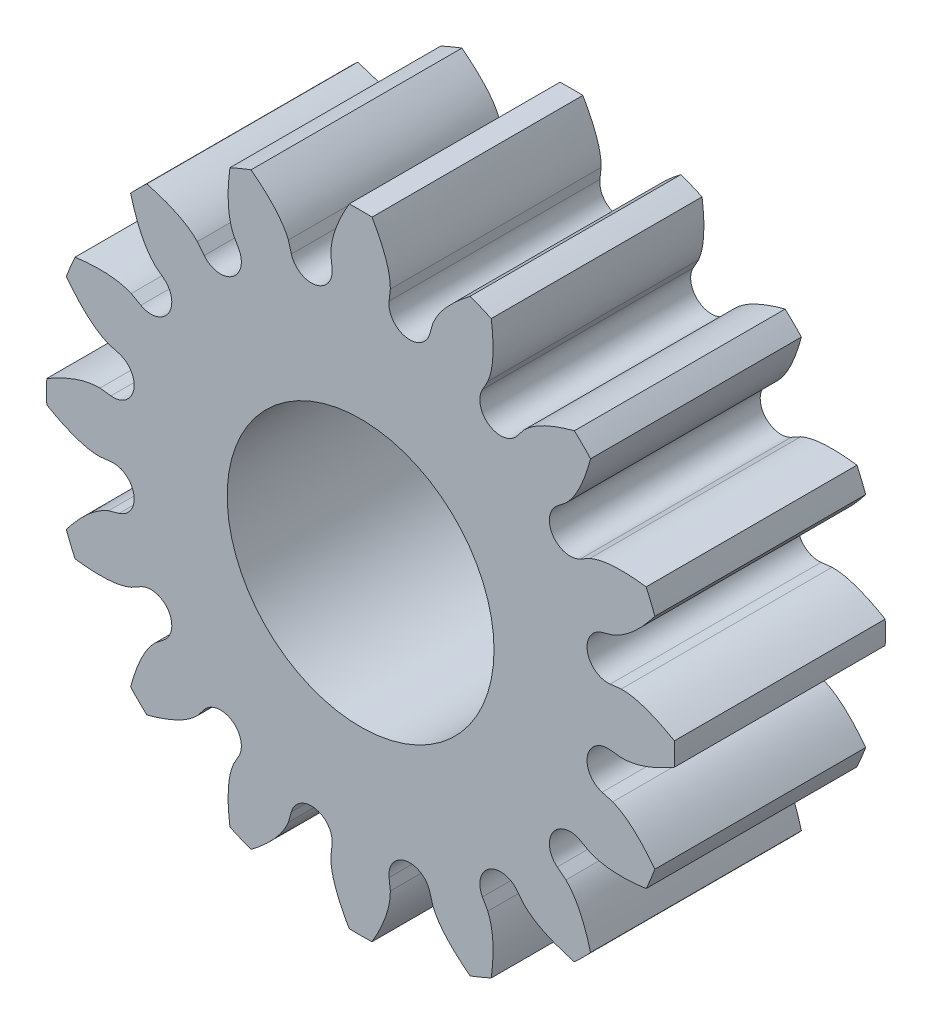
SolidWorks part; units mm, degrees
material "PE Low/Medium Density"
ref_plane "Front Plane" through (0, 0, 0) normal (0, 0, 1) x (1, 0, 0)
ref_plane "Top Plane" through (0, 0, 0) normal (0, 1, 0) x (1, 0, 0)
ref_plane "Right Plane" through (0, 0, 0) normal (1, 0, 0) x (0, 0, -1)
sketch "Involute construction sketch" plane through (0, 0, 0) normal (0, 0, 1) x (1, 0, 0)
  line L0 (0, 0) -> (-1.7884, 3.29) construction
  line L1 (0, 0) -> (-1.0853, 3.5839) construction
  line L2 (0, 0) -> (-0.3374, 3.7294) construction
  line L3 (0, 0) -> (0.4246, 3.7205) construction
  line L4 (-2.9462, 2.3113) -> (-2.4174, 2.8599) construction
  line L5 (-2.4174, 2.8599) -> (-1.7884, 3.29) construction
  line L6 (-1.7884, 3.29) -> (-1.0853, 3.5839) construction
  line L7 (0, 0) -> (-2.4174, 2.8599) construction
  line L8 (0, 0) -> (-2.9462, 2.3113) construction
  line L9 (-1.0853, 3.5839) -> (-0.3374, 3.7294) construction
  line L10 (-0.3374, 3.7294) -> (0.4246, 3.7205) construction
  line L11 (-2.9462, 2.3113) -> (-0.5946, 5.309) construction
  line L12 (-2.4174, 2.8599) -> (-0.0895, 4.8275) construction
  line L13 (-1.7884, 3.29) -> (0.2201, 4.3818) construction
  line L14 (-1.0853, 3.5839) -> (0.3732, 4.0256) construction
  line L15 (-0.3374, 3.7294) -> (0.4215, 3.7981) construction
  line L17 (0, 0) -> (0, 5.7859) construction
  line L18 (0, 0) -> (0.3906, 3.9658) construction
  line L19 (0, 0) -> (0.6442, 3.2386) construction
  circle A0 centre (0, 0) radius 3.302 construction
  circle A1 centre (0, 0) radius 3.7447 construction
  circle A2 centre (0, 0) radius 3.985 construction
  circle A3 centre (0, 0) radius 4.4831 construction
  spline S0 degree 3 poles (0.4246, 3.7205) (0.4261, 3.8242) (0.3767, 4.0544) (0.1137, 4.6484) (-0.2724, 5.0543) (-0.5946, 5.309) knots 0 0 0 0 0.160054 0.360046 1 1 1 1 construction
  point P17 (0.1633, 4.4801)
  dimension "D1" = 6.604
  dimension "D2" = 7.4893
  dimension "D3" = 7.97
  dimension "D4" = 8.9662
  dimension "D5" = 0.762
  dimension "D6" = 1.524
  dimension "D7" = 2.286
  dimension "D8" = 3.048
  dimension "D9" = 3.81
  dimension "D10" = 5.625
  dimension "D11" = 11.25
sketch "Sketch2" plane through (0, 0, 0) normal (0, 0, 1) x (1, 0, 0)
  line L0 (0, 4.4831) -> (0, 3.302)
  line L1 (0, 0) -> (0, 5.7859) construction
  line L2 (0.4246, 3.7205) -> (0.4067, 3.564)
  line L3 (0, 0) -> (0.4246, 3.7205) construction
  circle A0 centre (0, 0) radius 4.4831 construction
  circle A1 centre (0, 0) radius 3.302 construction
  arc A2 (0, 4.4831) -> (0.1633, 4.4801) centre (0, 0) cw
  arc A3 (0, 3.302) -> (0.6442, 3.2386) centre (0, 0) cw
  arc A4 (0.4067, 3.564) -> (0.6442, 3.2386) centre (0.7022, 3.5302) ccw
  spline S0 degree 3 poles (0.4246, 3.7205) (0.4258, 3.8034) (0.3801, 4.0726) (0.2566, 4.3168) (0.1633, 4.4801) knots 0 0 0 0 0.305961 1 1 1 1
sketch "Sketch3" plane through (0, 0, 0) normal (0, 0, 1) x (1, 0, 0)
  circle A0 centre (0, 0) radius 3.302
  circle A1 centre (0, 0) radius 1.905
  dimension "D1" = 6.604
  dimension "D2" = 3.81
extrude "Base" add sketch "Sketch3" along normal blind 3.0099
extrude "Half tooth" add sketch "Sketch2" along normal up to surface (3.0099 mm away) up to face at (3.302, 0, 3.0099)
ref_plane "Midplane of half tooth" through (0, 0, 0) normal (-1, 0, 0) x (0, 0, 1)
mirror "Mirror of half tooth" about plane through (0, 0, 0) normal (-1, 0, 0) of "Half tooth"
pattern_circular "Pattern of tooth" count 16 over 360 about axis through (0, 0, 3.0099) along (0, 0, 1) of "Half tooth", "Mirror of half tooth"
equation "\"radtodeg\"= 180 / PI'radian to degree conversion [ ]"
equation "\"phi\"= 20'pressure angle [deg]"
equation "\"N\"= 16'number of teeth [teeth]"
equation "\"A\"= 0.353in'diameter of addendum circle [inch]"
equation "\"B\"= 0.260in'diameter of dedendum circle [inch]"
equation "\"P\"= ( \"N\" + 2 ) / \"A\"'diametral pitch [teeth/inch]"
equation "\"d\"= \"N\" / \"P\"'diameter of pitch circle [inch]"
equation "\"cp\"= PI / \"P\"'circular pitch [inch/teeth]"
equation "\"add\"= 1 / \"P\"'addendum [inch]"
equation "\"ded\"= - ( \"B\" - \"d\" ) / 2'dedendum [inch]"
equation "\"clear\"= \"ded\" - \"add\"'clearance [inch]"
equation "\"C\"= \"B\" + 2 * \"clear\"'diameter of clearance circle [inch]"
equation "\"h\"= \"add\" + \"ded\"'tooth height / whole depth [inch]"
equation "\"s\"= \"d\" * cos ( \"phi\" * 1 / \"radtodeg\" )'diameter of base circle [inch]"
equation "\"t\"= ( PI / 2 ) / \"P\"'tooth width at diameter of pitch circle diameter [inch]"
equation "\"alpha\"= ( \"t\" / ( \"d\" / 2 ) * \"radtodeg\" ) / 2'arc angle for half of tooth width at pitch circle diameter [inch]"
equation "\"bore\"= 0.15'bore of hub [inch]"
equation "\"D4@Involute construction sketch\"= \"A\"'addendum circle"
equation "\"D3@Involute construction sketch\"= \"d\"'pitch circle"
equation "\"D2@Involute construction sketch\"= \"s\"'base circle"
equation "\"D1@Involute construction sketch\"= \"B\"'dedendum circle"
equation "\"seg\"= \"D5@Involute construction sketch\"'size of one involute segment [inch]"
equation "\"D6@Involute construction sketch\"=2*\"seg\""
equation "\"D7@Involute construction sketch\"=3*\"seg\""
equation "\"D8@Involute construction sketch\"=4*\"seg\""
equation "\"D9@Involute construction sketch\"=5*\"seg\""
equation "\"D10@Involute construction sketch\"=\"alpha\""
equation "\"D11@Involute construction sketch\"=2*\"alpha\""
equation "\"D1@Sketch3\"=\"B\""
equation "\"D2@Sketch3\"=\"bore\""
